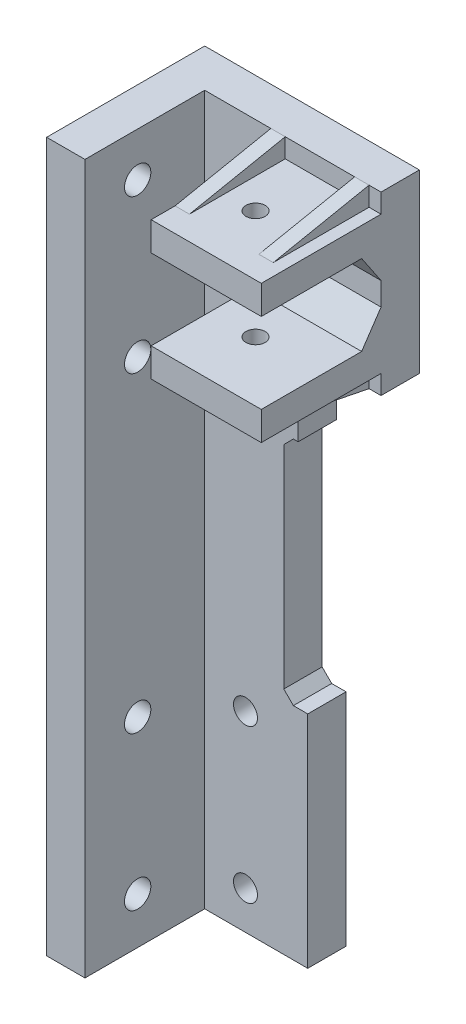
SolidWorks part; units mm, degrees
ref_plane "Plan de face" through (0, 0, 0) normal (0, 0, 1) x (1, 0, 0)
ref_plane "Plan de dessus" through (0, 0, 0) normal (0, 1, 0) x (1, 0, 0)
ref_plane "Plan de droite" through (0, 0, 0) normal (1, 0, 0) x (0, 0, -1)
sketch "Sketch1" plane through (0, 0, 0) normal (0, 0, 1) x (1, 0, 0)
  line L1 (0, 0) -> (-24.51, 0)
  line L2 (0, 0) -> (0, 148)
  line L3 (0, 148) -> (-24.51, 148)
  line L4 (-24.51, 0) -> (-24.51, 148)
  dimension "D1" = 24.51
  dimension "D2" = 148
extrude "Boss-Extrude1" add sketch "Sketch1" along normal blind 8
sketch "Sketch2" plane through (0, 0, 8) normal (0, 0, 1) x (1, 0, 0)
  line L0 (-24.51, 0) -> (0, 0) construction
  line L1 (-24.51, 148) -> (-16.51, 148)
  line L2 (-24.51, 148) -> (-24.51, 0)
  line L3 (-24.51, 0) -> (-16.51, 0)
  line L4 (-16.51, 148) -> (-16.51, 0)
  dimension "D1" = 8
extrude "Boss-Extrude2" add sketch "Sketch2" along normal blind 25
sketch "Sketch4" plane through (0, 0, 0) normal (0, 0, -1) x (-1, 0, 0)
  line L0 (0, 0) -> (0, 148) construction
  line L1 (0, 148) -> (-20.3, 148)
  line L2 (0, 148) -> (0, 111.2)
  line L3 (0, 111.2) -> (-20.3, 111.2)
  line L4 (-20.3, 148) -> (-20.3, 111.2)
  line L6 (0, 148) -> (24.51, 148) construction
  dimension "D1" = 36.8
  dimension "D2" = 20.3
extrude "Boss-Extrude3" add sketch "Sketch4" against normal up to surface (8 mm away) up to face at (-8.255, 55.5, 8)
sketch "Sketch5" plane through (0, 0, 8) normal (0, 0, 1) x (1, 0, 0)
  line L0 (20.3, 148) -> (20.3, 111.2) construction
  line L1 (20.3, 115.2) -> (-2.7, 115.2)
  line L2 (20.3, 115.2) -> (20.3, 121.2)
  line L3 (20.3, 121.2) -> (-2.7, 121.2)
  line L4 (-2.7, 115.2) -> (-2.7, 121.2)
  line L6 (20.3, 111.2) -> (0, 111.2) construction
  line L8 (20.3, 148) -> (20.3, 111.2) construction
  line L9 (20.3, 144) -> (-2.7, 144)
  line L10 (20.3, 144) -> (20.3, 138)
  line L11 (20.3, 138) -> (-2.7, 138)
  line L12 (-2.7, 144) -> (-2.7, 138)
  line L13 (20.3, 148) -> (-16.51, 148) construction
  dimension "D1" = 6
  dimension "D2" = 4
  dimension "D3" = 23
  dimension "D4" = 6
  dimension "D5" = 4
extrude "Boss-Extrude4" add sketch "Sketch5" along normal blind 25 contours L3 L4 L1 L2
sketch "Sketch6" plane through (0, 144, 0) normal (0, 1, 0) x (1, 0, 0)
  line L3 (20.3, -33) -> (20.3, -8) construction
  circle A0 centre (6.6, -20.5) radius 2
  dimension "D1" = 4
  dimension "D2" = 13.7
extrude "Cut-Extrude2" cut sketch "Sketch6" against normal up to surface (28.8 mm away) up to face at (8.8, 115.2, 20.5)
ref_plane "Plane1" through (16.3, 0, 0) normal (1, 0, 0) x (0, 0, -1)
sketch "Sketch8" plane through (16.3, 0, 0) normal (1, 0, 0) x (0, 0, -1)
  line L0 (-8, 148) -> (-28, 144)
  line L1 (-33, 144) -> (-8, 144) construction
  line L2 (-33, 0) -> (-33, 148) construction
  dimension "D1" = 5
rib "Rib1" sketch "Sketch8" sketch "Sketch8" thickness 3 extrusion direction parallel to sketch draft on no parameters "D1"=3
ref_plane "Plane2" through (0, 129.6, 0) normal (0, 1, 0) x (1, 0, 0)
mirror "Mirror1" about plane through (0, 129.6, 0) normal (0, 1, 0) of "Rib1"
ref_plane "Plane3" through (7.55, 0, 0) normal (-1, 0, 0) x (0, 0, 1)
mirror "Mirror2" about plane through (7.55, 0, 0) normal (-1, 0, 0) of "Mirror1", "Rib1"
sketch "Sketch3" plane through (0, 0, 8) normal (0, 0, 1) x (1, 0, 0)
  line L0 (0, 0) -> (0, 111.2) construction
  line L1 (0, 0) -> (0, 111.2) construction
  line L4 (-24.51, 0) -> (0, 0) construction
  circle A0 centre (-8, 8) radius 2.5
  circle A1 centre (-8, 40) radius 2.5
  circle A2 centre (-8, 100) radius 2.5
  circle A3 centre (-8, 132) radius 2.5
  dimension "D1" = 5
  dimension "D2" = 5
  dimension "D9" = 5
  dimension "D10" = 5
  dimension "D3" = 32
  dimension "D4" = 8
  dimension "D5" = 8
  dimension "D6" = 60
  dimension "D7" = 32
  dimension "D8" = 8
extrude "Cut-Extrude1" cut sketch "Sketch3" against normal blind 10
sketch "Sketch12" plane through (-24.51, 0, 0) normal (-1, 0, 0) x (0, 0, 1)
  circle A0 centre (22, 138.8) radius 2.75
  circle A1 centre (22, 106.8) radius 2.75
  circle A2 centre (22, 41.7) radius 2.75
  circle A3 centre (22, 9.7) radius 2.75
  dimension "D1" = 5.5
  dimension "D2" = 5.5
  dimension "D4" = 5.5
  dimension "D5" = 5.5
  dimension "D3" = 32
  dimension "D6" = 65.1
  dimension "D7" = 32
extrude "Cut-Extrude3" cut sketch "Sketch12" against normal up to surface (8 mm away) up to face at (-16.51, 55.5, 26.75)
sketch "Sketch13" plane through (0, 0, 0) normal (0, 0, -1) x (-1, 0, 0)
  line L1 (0, 0) -> (-5, 0)
  line L2 (0, 0) -> (0, 46)
  line L3 (0, 46) -> (-5, 46)
  line L4 (-5, 0) -> (-5, 46)
  dimension "D1" = 5
  dimension "D2" = 46
extrude "Boss-Extrude5" add sketch "Sketch13" against normal up to surface (8 mm away) up to face at (19.3625, 146, 8)
sketch "Sketch14" plane through (0, 0, 0) normal (0, 0, -1) x (-1, 0, 0)
  line L1 (0, 111.2) -> (-3, 111.2)
  line L2 (0, 111.2) -> (0, 94.2)
  line L3 (0, 94.2) -> (-3, 94.2)
  line L4 (-3, 111.2) -> (-3, 94.2)
  dimension "D1" = 3
  dimension "D2" = 17
extrude "Boss-Extrude6" add sketch "Sketch14" against normal up to surface (8 mm away) up to face at (19.3625, 146, 8)
chamfer "Chamfer1" distance 2 angle 45 3 edges at (0, 46, 4) (3, 111.2, 4) (0, 94.2, 4)
chamfer "Chamfer2" distance 6 angle 34 2 edges at (8.8, 121.2, 8) (8.8, 138, 8)
sketch "Sketch15" plane through (20.3, 0, 0) normal (1, 0, 0) x (0, 0, -1)
  line L0 (-33, 0) -> (-33, 148) construction
  line L1 (0, 148) -> (-33, 148)
  line L2 (0, 148) -> (0, 52)
  line L3 (0, 52) -> (-33, 52)
  line L4 (-33, 148) -> (-33, 52)
  dimension "D1" = 96
extrude "Cut-Extrude4" [suppressed] cut sketch "Sketch15" against normal blind 45
equation "\"D9@Sketch3\"=\"D1@Sketch3\""
equation "\"D10@Sketch3\"=\"D1@Sketch3\""
